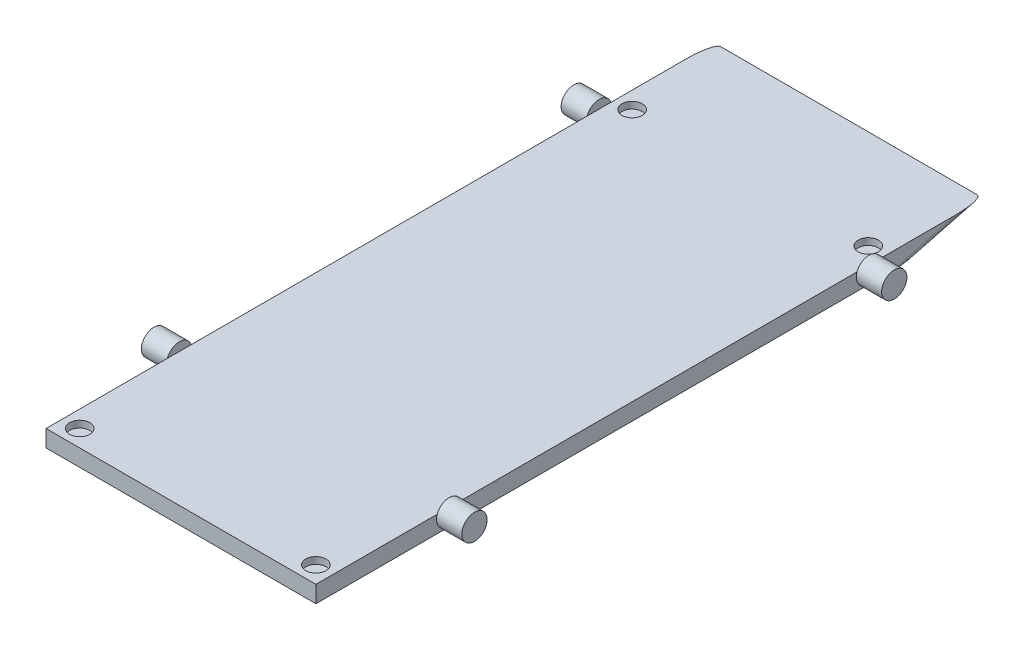
SolidWorks part; units mm, degrees
ref_plane "Front Plane" through (0, 0, 0) normal (0, 0, 1) x (1, 0, 0)
ref_plane "Top Plane" through (0, 0, 0) normal (0, 1, 0) x (1, 0, 0)
ref_plane "Right Plane" through (0, 0, 0) normal (1, 0, 0) x (0, 0, -1)
sketch "Sketch1" plane through (0, 0, 0) normal (0, 1, 0) x (1, 0, 0)
  line L1 (-40, 99) -> (40, 99)
  line L2 (-40, 99) -> (-40, -99)
  line L3 (-40, -99) -> (40, -99)
  line L4 (40, 99) -> (40, -99)
  line L5 (-40, 99) -> (40, -99) construction
  line L6 (-40, -99) -> (40, 99) construction
  point P0 (0, 0)
  dimension "D1" = 198
  dimension "D2" = 80
extrude "Boss-Extrude1" add sketch "Sketch1" along normal blind 5
sketch "Sketch2" plane through (-40, 0, 0) normal (-1, 0, 0) x (0, 0, 1)
  line L0 (99, 0) -> (-99, 0)
  line L1 (-64.9289, 5) -> (-99, 5)
  line L2 (-99, 5) -> (99, 5) construction
  line L3 (99, 5) -> (59.5, 5)
  line L4 (-99, 2.5) -> (-64.9289, 2.5) construction
  line L5 (-99, 5) -> (-99, 0) construction
  line L6 (-64.9289, 2.5) -> (-64.9289, 5) construction
  circle A0 centre (-64.9289, 3.75) radius 3.75
  circle A1 centre (59.5, 3.75) radius 3.75
  point P3 (0, 0)
  dimension "D3" = 7.5
  dimension "D4" = 7.5
  dimension "D1" = 34.0711
  dimension "D2" = 39.5
extrude "Boss-Extrude2" add sketch "Sketch2" along normal blind 7.5 contours L5 A0 | L3 A1 L5 | L5 A1 L3
mirror "Mirror1" about plane through (0, 0, 0) normal (1, 0, 0) of "Boss-Extrude2"
sketch "Sketch3" plane through (-40, 0, 0) normal (-1, 0, 0) x (0, 0, 1)
  line L0 (-99, 5) -> (-72.9325, -1.7591)
  line L1 (-72.9325, -1.7591) -> (-103.7993, -1.7591)
  line L2 (-103.7993, -1.7591) -> (-99, 5)
  dimension "D1" = 165.464
  dimension "D2" = 125.377
  dimension "D3" = 30.8668
extrude "Cut-Extrude1" cut sketch "Sketch3" against normal through all
fillet "Fillet2" radius 2 2 edges at (40, 2.5, -89.3584) (-40, 2.5, -89.3584)
sketch "Sketch4" plane through (0, 0, 0) normal (0, -1, 0) x (1, 0, 0)
  line L0 (-40, -64.9289) -> (-40, 59.5) construction
  line L1 (35, -69.7169) -> (-35, -69.7169) construction
  line L2 (35, -69.7169) -> (35, 94) construction
  line L3 (35, 94) -> (-35, 94) construction
  line L4 (-35, -69.7169) -> (-35, 94) construction
  line L5 (40, 59.5) -> (40, -64.9289) construction
  line L6 (-40, 99) -> (40, 99) construction
  line L7 (-38, -79.7169) -> (38, -79.7169) construction
  circle A0 centre (-35, -69.7169) radius 3
  circle A1 centre (35, -69.7169) radius 3
  circle A2 centre (-35, 94) radius 3
  circle A3 centre (35, 94) radius 3
  dimension "D5" = 6
  dimension "D1" = 5
  dimension "D2" = 5
  dimension "D3" = 5
  dimension "D4" = 10
extrude "Cut-Extrude2" cut sketch "Sketch4" along normal blind 2 from surface at -5 starting at face at (0, 5, -14.7914)
